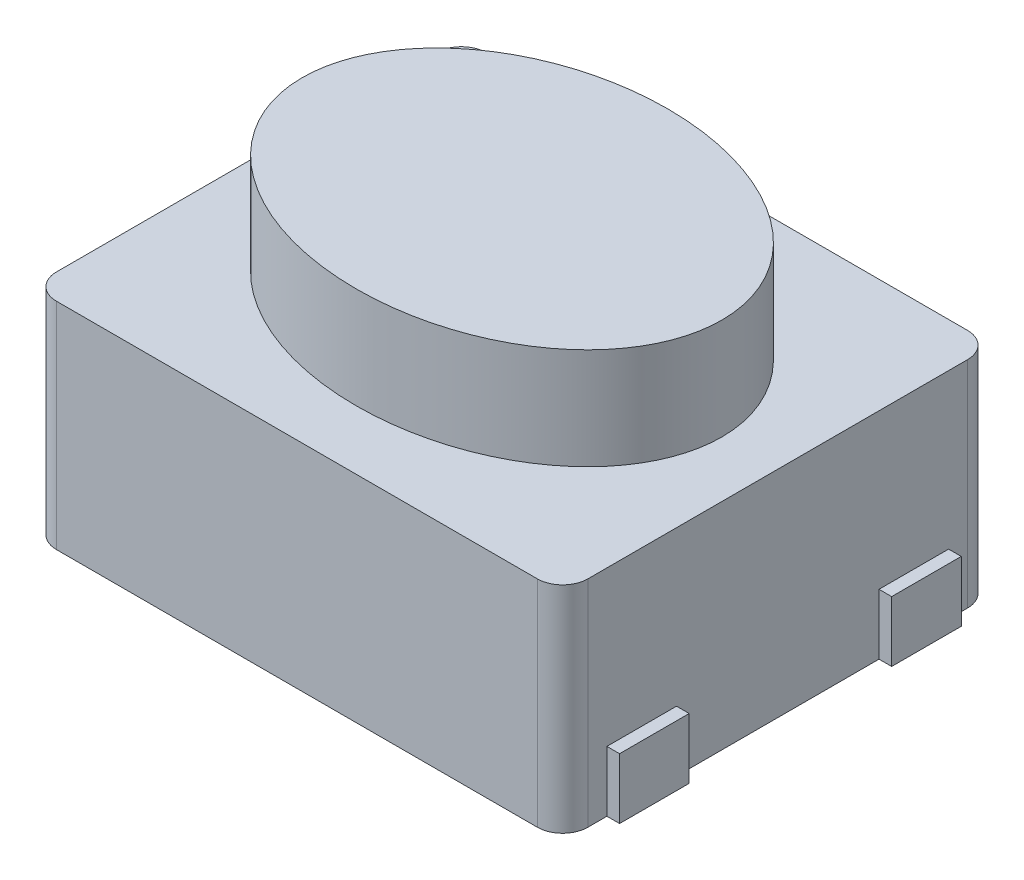
SolidWorks part; units mm, degrees
ref_plane "前视基准面" through (0, 0, 0) normal (0, 0, 1) x (1, 0, 0)
ref_plane "上视基准面" through (0, 0, 0) normal (0, 1, 0) x (1, 0, 0)
ref_plane "右视基准面" through (0, 0, 0) normal (1, 0, 0) x (0, 0, -1)
sketch "草图1" plane through (0, 0, 0) normal (0, 1, 0) x (1, 0, 0)
  line L1 (-2.1, -1.7) -> (2.1, -1.7)
  line L2 (-2.1, -1.7) -> (-2.1, 1.7)
  line L3 (-2.1, 1.7) -> (2.1, 1.7)
  line L4 (2.1, -1.7) -> (2.1, 1.7)
  line L5 (-2.1, -1.7) -> (2.1, 1.7) construction
  line L6 (-2.1, 1.7) -> (2.1, -1.7) construction
  point P0 (0, 0)
  dimension "D1" = 4.2
  dimension "D2" = 3.4
extrude "凸台-拉伸1" add sketch "草图1" along normal blind 1.7
sketch "草图2" plane through (0, 1.7, 0) normal (0, 1, 0) x (1, 0, 0)
  ellipse E0 centre (0, 0) end of major axis (1.6587, 0) minor radius 1.2317
extrude "凸台-拉伸2" add sketch "草图2" along normal blind 0.8
fillet "圆角1" radius 0.2 4 edges at (2.1, 0.85, -1.7) (-2.1, 0.85, -1.7) (2.1, 0.85, 1.7) (-2.1, 0.85, 1.7)
sketch "草图3" plane through (-2.1, 0, 0) normal (-1, 0, 0) x (0, 0, 1)
  line L0 (-1.5, 0) -> (1.5, 0) construction
  line L1 (-1.35, 0.4783) -> (-0.8, 0.4783)
  line L2 (-1.35, 0.4783) -> (-1.35, 0)
  line L3 (-1.35, 0) -> (-0.8, 0)
  line L4 (-0.8, 0.4783) -> (-0.8, 0)
  line L5 (0, -0.1162) -> (0, 1.0981) construction
  line L6 (1.35, 0) -> (0.8, 0)
  line L7 (0.8, 0.4783) -> (0.8, 0)
  line L8 (1.35, 0.4783) -> (0.8, 0.4783)
  line L9 (1.35, 0.4783) -> (1.35, 0)
  dimension "D1" = 0.8
  dimension "D2" = 1.35
extrude "凸台-拉伸3" add sketch "草图3" along normal blind 0.1
mirror "镜向1" about plane through (0, 0, 0) normal (1, 0, 0) of "凸台-拉伸3"
